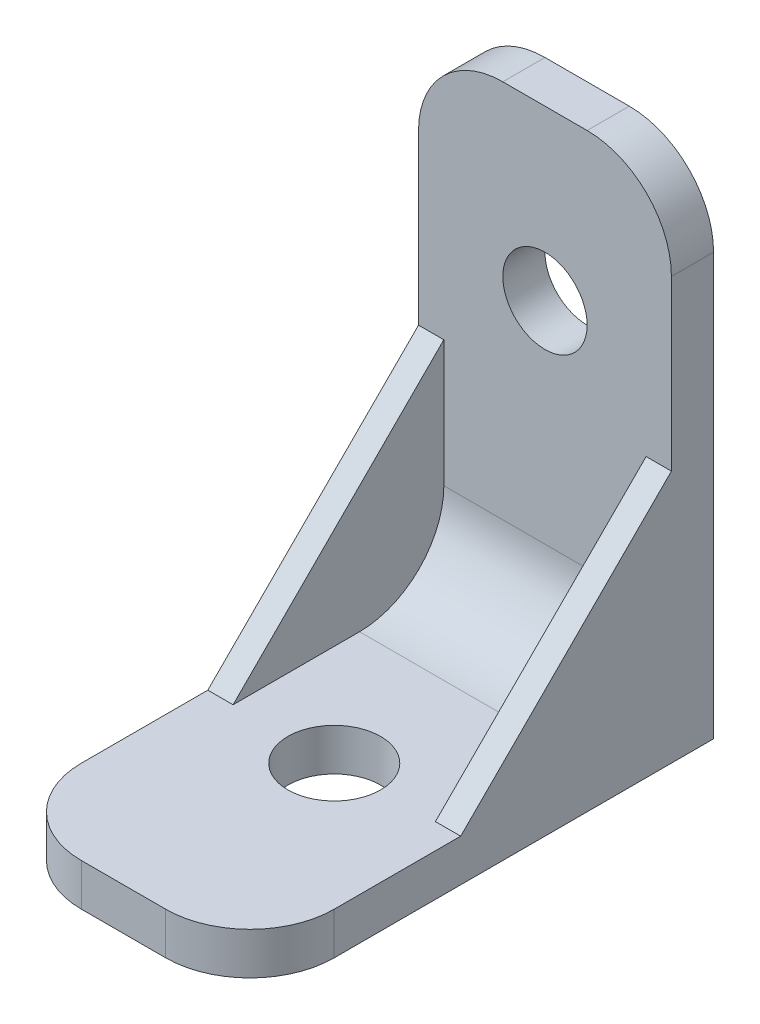
SolidWorks part; units mm, degrees
ref_plane "Front Plane" through (0, 0, 0) normal (0, 0, 1) x (1, 0, 0)
ref_plane "Top Plane" through (0, 0, 0) normal (0, 1, 0) x (1, 0, 0)
ref_plane "Right Plane" through (0, 0, 0) normal (1, 0, 0) x (0, 0, -1)
sketch "Sketch1" plane through (0, 0, 0) normal (1, 0, 0) x (0, 0, -1)
  line L0 (-55, 5) -> (-5, 5)
  line L1 (-5, 5) -> (-5, 60)
  line L2 (-5, 60) -> (0, 60)
  line L3 (0, 60) -> (0, 0)
  line L4 (0, 0) -> (-55, 0)
  line L5 (-55, 0) -> (-55, 5)
  dimension "D1" = 5
  dimension "D2" = 55
  dimension "D3" = 60
  dimension "D4" = 55
  dimension "D5" = 50
extrude "Boss-Extrude1" add sketch "Sketch1" along normal mid plane 30
sketch "Sketch2" plane through (0, 5, 0) normal (0, 1, 0) x (1, 0, 0)
  line L0 (15, -5) -> (-15, -5) construction
  circle A0 centre (0, -30) radius 5.5
  point P5 (0, -5)
  dimension "D1" = 11
  dimension "D2" = 25
extrude "Cut-Extrude1" cut sketch "Sketch2" against normal blind 30
sketch "Sketch3" plane through (0, 0, 5) normal (0, 0, 1) x (1, 0, 0)
  line L0 (15, 60) -> (-15, 60) construction
  line L2 (15, 5) -> (-15, 5) construction
  circle A0 centre (0, 40) radius 5
  point P5 (0, 60)
  dimension "D1" = 10
  dimension "D2" = 35
  dimension "D3" = 20
extrude "Cut-Extrude2" cut sketch "Sketch3" against normal blind 30
fillet "Fillet1" radius 10 4 edges at (-15, 60, 2.5) (15, 60, 2.5) (-15, 2.5, 55) (15, 2.5, 55)
sketch "Sketch4" plane through (-15, 0, 0) normal (-1, 0, 0) x (0, 0, 1)
  line L0 (30, 5) -> (5, 30)
  line L1 (5, 5) -> (45, 5) construction
  line L2 (5, 50) -> (5, 5) construction
  line L3 (5, 30) -> (5, 5)
  line L4 (5, 5) -> (30, 5)
  dimension "D1" = 25
extrude "Boss-Extrude2" add sketch "Sketch4" against normal blind 3
mirror "Mirror1" about plane through (0, 0, 0) normal (1, 0, 0) of "Boss-Extrude2"
fillet "Fillet2" radius 10 1 edges at (0, 5, 5)
